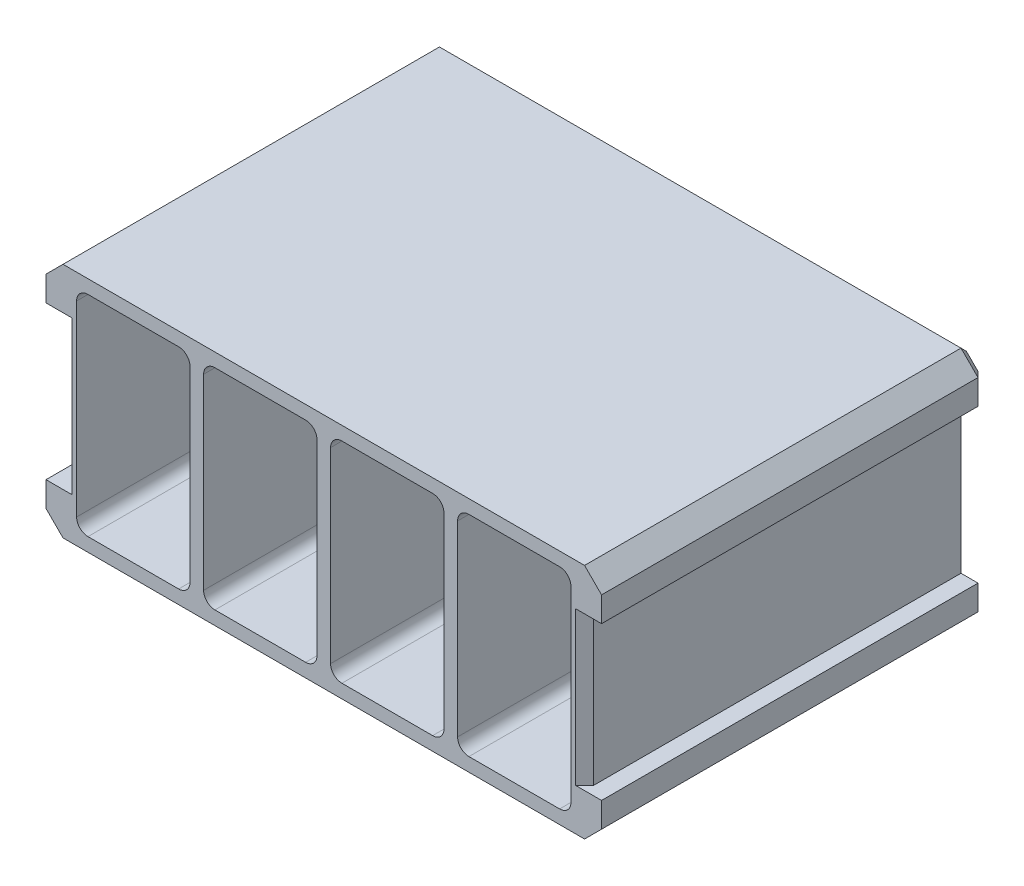
SolidWorks part; units mm, degrees
ref_plane "Front Plane" through (0, 0, 0) normal (0, 0, 1) x (1, 0, 0)
ref_plane "Top Plane" through (0, 0, 0) normal (0, 1, 0) x (1, 0, 0)
ref_plane "Right Plane" through (0, 0, 0) normal (1, 0, 0) x (0, 0, -1)
sketch "Sketch1" plane through (0, 0, 0) normal (0, 0, 1) x (1, 0, 0)
  line L0 (12.4, -18.5) -> (12.4, 18.5)
  line L1 (-10, -18.5) -> (10, -18.5)
  line L2 (-10, -18.5) -> (-10, 18.5)
  line L3 (-10, 18.5) -> (10, 18.5)
  line L4 (10, -18.5) -> (10, 18.5)
  line L5 (0, 18.5) -> (0, -18.5) construction
  line L6 (-10, 0) -> (10, 0) construction
  line L7 (12.4, -18.5) -> (32.4, -18.5)
  line L8 (32.4, -18.5) -> (32.4, 18.5)
  line L9 (12.4, 18.5) -> (32.4, 18.5)
  line L10 (34.8, -18.5) -> (34.8, 18.5)
  line L11 (34.8, -18.5) -> (54.8, -18.5)
  line L12 (54.8, -18.5) -> (54.8, 18.5)
  line L13 (34.8, 18.5) -> (54.8, 18.5)
  line L14 (57.2, -18.5) -> (57.2, 18.5)
  line L15 (57.2, -18.5) -> (77.2, -18.5)
  line L16 (77.2, -18.5) -> (77.2, 18.5)
  line L17 (57.2, 18.5) -> (77.2, 18.5)
  line L18 (-10, 18.5) -> (-10, 20.9) construction
  line L19 (-12.4, 20.9) -> (79.6, 20.9)
  line L20 (-12.4, 20.9) -> (-12.4, -20.9)
  line L21 (-12.4, -20.9) -> (79.6, -20.9)
  line L22 (79.6, 20.9) -> (79.6, -20.9)
  line L23 (33.6, -20.9) -> (33.6, 20.9) construction
  line L24 (-12.4, 0) -> (79.6, 0) construction
  line L25 (-10, 18.5) -> (-12.4, 18.5) construction
  line L26 (77.2, -18.5) -> (79.6, -18.5) construction
  line L27 (77.2, -18.5) -> (77.2, -20.9) construction
  point P0 (0, 0)
  point P20 (0, 0)
  point P410 (33.6, 0)
  dimension "D1" = 37
  dimension "D2" = 20
  dimension "D4" = 2.4
  dimension "D5" = 2.4
  dimension "D3" = 4
extrude "Boss-Extrude1" add sketch "Sketch1" along normal blind 65
sketch "Sketch2" plane through (0, 0, 0) normal (0, 0, -1) x (-1, 0, 0)
  line L1 (12.4, 20.9) -> (-79.6, 20.9)
  line L2 (12.4, 20.9) -> (12.4, -20.9)
  line L3 (12.4, -20.9) -> (-79.6, -20.9)
  line L4 (-79.6, 20.9) -> (-79.6, -20.9)
  line L5 (-33.6, -20.9) -> (-33.6, 20.9) construction
  line L6 (12.4, 0) -> (-79.6, 0) construction
  point P404 (-33.6, 0)
extrude "Boss-Extrude2" add sketch "Sketch2" along normal blind 3
ref_plane "Plane1" through (33.6, 0, 0) normal (-1, 0, 0) x (0, 0, 1)
sketch "Sketch4" plane through (0, 0, -3) normal (0, 0, -1) x (-1, 0, 0)
  line L0 (-79.6, 20.9) -> (-79.6, 13.5)
  line L1 (-79.6, 20.9) -> (-79.6, -20.9) construction
  line L2 (-79.6, 13.5) -> (-82.6, 13.5)
  line L3 (-82.6, 13.5) -> (-82.6, 17.9)
  line L4 (-82.6, 17.9) -> (-79.6, 20.9)
  line L5 (-1070.5716, 0) -> (48929.4284, 0) construction
  line L7 (-82.6, -13.5) -> (-82.6, -17.9)
  line L8 (-79.6, -13.5) -> (-82.6, -13.5)
  line L9 (-79.6, -20.9) -> (-79.6, -13.5)
  line L10 (-82.6, -17.9) -> (-79.6, -20.9)
  dimension "D1" = 45
  dimension "D2" = 3
  dimension "D3" = 27
extrude "Boss-Extrude3" add sketch "Sketch4" against normal up to surface (68 mm away) up to face at (33.6, 0, 65)
mirror "Mirror1" about plane through (33.6, 0, 0) normal (-1, 0, 0) of "Boss-Extrude3"
chamfer "Chamfer4" distance 1.6 angle 45 16 edges at (81.1, -19.4, -3) (82.6, -15.7, -3) (81.1, -13.5, -3) (79.6, 0, -3) (81.1, 13.5, -3) (82.6, 15.7, -3) (81.1, 19.4, -3) (33.6, 20.9, -3) (-13.9, 19.4, -3) (-15.4, 15.7, -3) (-13.9, 13.5, -3) (-12.4, 0, -3) (-13.9, -13.5, -3) (-15.4, -15.7, -3) (-13.9, -19.4, -3) (33.6, -20.9, -3)
sketch "Sketch3" plane through (0, 0, 0) normal (0, 0, 1) x (1, 0, 0)
  line L1 (57.2, 18.5) -> (77.2, 18.5) construction
  circle A0 centre (0, 0) radius 7.5
  circle A1 centre (22.4, 0) radius 7.5
  circle A2 centre (44.8, 0) radius 7.5
  circle A3 centre (67.2, 0) radius 7.5
  point P12 (67.2, 18.5)
  dimension "D2" = 15
  dimension "D1" = 4
extrude "Cut-Extrude1" cut sketch "Sketch3" against normal through all
fillet "Fillet1" radius 2 16 edges at (77.2, -18.5, 32.5) (57.2, -18.5, 32.5) (54.8, -18.5, 32.5) (34.8, -18.5, 32.5) (32.4, -18.5, 32.5) (12.4, -18.5, 32.5) (10, -18.5, 32.5) (-10, -18.5, 32.5) (57.2, 18.5, 32.5) (34.8, 18.5, 32.5) (77.2, 18.5, 32.5) (54.8, 18.5, 32.5) (32.4, 18.5, 32.5) (12.4, 18.5, 32.5) (10, 18.5, 32.5) (-10, 18.5, 32.5)
fillet "Fillet2" radius 2 32 edges at (76.6142, 17.9142, 0) (77.2, 0, 0) (76.6142, -17.9142, 0) (67.2, -18.5, 0) (57.7858, -17.9142, 0) (57.2, 0, 0) (57.7858, 17.9142, 0) (54.2142, 17.9142, 0) (54.8, 0, 0) (54.2142, -17.9142, 0) (44.8, -18.5, 0) (35.3858, -17.9142, 0) (34.8, 0, 0) (35.3858, 17.9142, 0) (31.8142, 17.9142, 0) (32.4, 0, 0) (31.8142, -17.9142, 0) (22.4, -18.5, 0) (12.9858, -17.9142, 0) (12.4, 0, 0) (12.9858, 17.9142, 0) (9.4142, 17.9142, 0) (10, 0, 0) (9.4142, -17.9142, 0) (0, -18.5, 0) (-9.4142, -17.9142, 0) (-10, 0, 0) (-9.4142, 17.9142, 0) (67.2, 18.5, 0) (44.8, 18.5, 0) (22.4, 18.5, 0) (0, 18.5, 0)
chamfer "Chamfer5" distance 1.6 angle 45 2 edges at (79.6, 0, 65) (-12.4, 0, 65)
